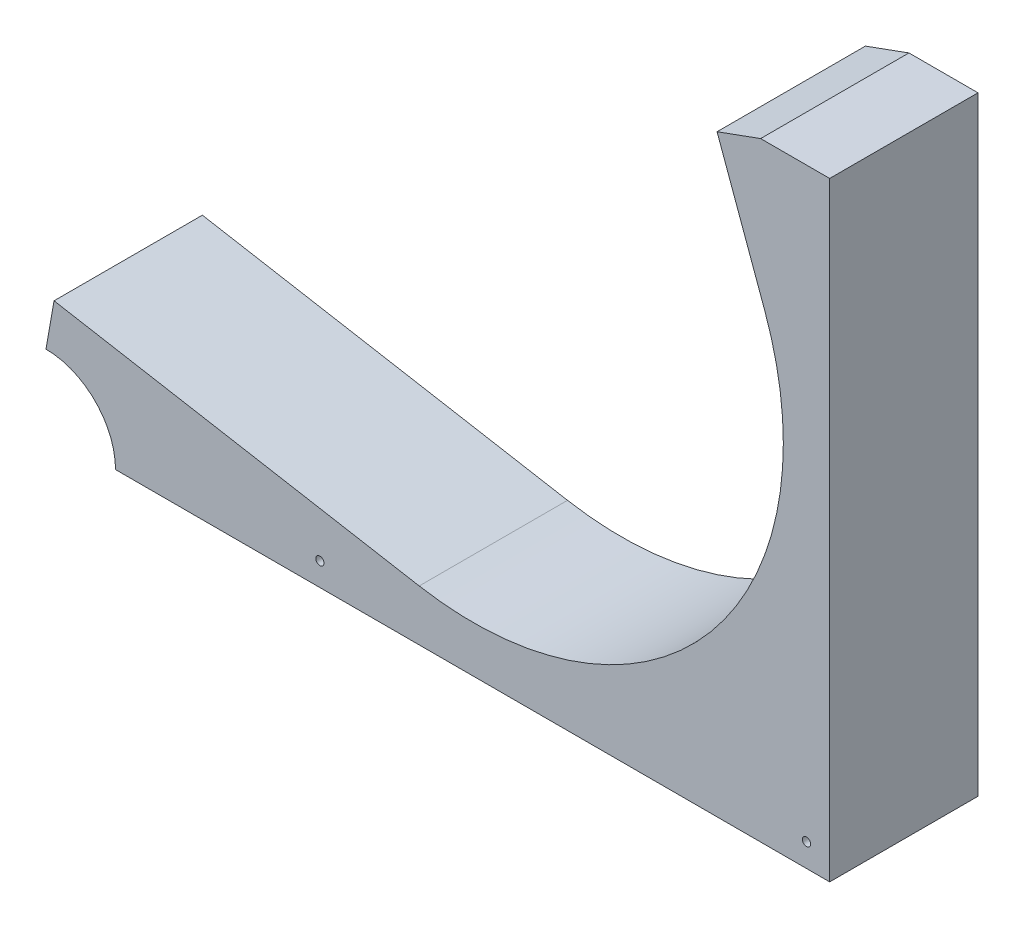
SolidWorks part; units mm, degrees
ref_plane "Front Plane" through (0, 0, 0) normal (0, 0, 1) x (1, 0, 0)
ref_plane "Top Plane" through (0, 0, 0) normal (0, 1, 0) x (1, 0, 0)
ref_plane "Right Plane" through (0, 0, 0) normal (1, 0, 0) x (0, 0, -1)
sketch "Sketch2" plane through (0, 0, 0) normal (0, 0, 1) x (1, 0, 0)
  line L0 (0, 0) -> (69.3863, 0)
  line L1 (69.3863, 0) -> (61.2697, 22.3003)
  line L2 (0, -65.2018) -> (-81.9123, -65.2018) construction
  line L3 (-11.3222, -64.2112) -> (-111.3786, -46.5686)
  line L4 (61.2697, 22.3003) -> (48.2387, 58.1026)
  arc A0 (61.2697, 22.3003) -> (-11.3222, -64.2112) centre (0, 0) cw
  circle A1 centre (0, 0) radius 45.212 construction
  point P11 (-11.3222, -64.2112)
  dimension "D3" = 90.424
  dimension "D1" = 65.2018
  dimension "D2" = 70
  dimension "D4" = 10
  dimension "D5" = 38.1
  dimension "D6" = 101.6
sketch3d "3DSketch1"
  line L0 (-114.819, -66.0796, 0) -> (-111.3786, -46.5686, 0) construction
  line L1 (-117.0243, -78.5867, -20.32) -> (-114.819, -66.0796, -20.32)
  line L2 (-117.0243, -78.5867, -20.32) -> (-117.0243, -78.5867, 20.32)
  line L3 (-117.0243, -78.5867, 20.32) -> (-114.819, -66.0796, 20.32)
  line L4 (-114.819, -66.0796, -20.32) -> (-114.819, -66.0796, 20.32)
  line L5 (-117.0243, -78.5867, -20.32) -> (-114.819, -66.0796, 20.32) construction
  line L6 (-117.0243, -78.5867, 20.32) -> (-114.819, -66.0796, -20.32) construction
  line L7 (-11.3222, -64.2112, 0) -> (-111.3786, -46.5686, 0) construction
  line L8 (0, -65.2018, 0) -> (-81.9123, -65.2018, 0) construction
  point P4 (-115.9216, -72.3331, 0)
  dimension "D1" = 12.7
  dimension "D2" = 40.64
  dimension "D3" = 19.812
sweep "Sweep3" add profiles "3DSketch1" path "Sketch2"
sketch "Sketch5" plane through (0, 0, 20.32) normal (0, 0, 1) x (1, 0, 0)
  line L0 (-117.0243, -78.5867) -> (-117.0243, -97.7138)
  line L1 (-117.0243, -97.7138) -> (97.7138, -97.7138)
  line L2 (97.7138, -97.7138) -> (97.7138, 69.2224)
  line L3 (97.7138, 69.2224) -> (78.79, 69.2224)
  line L4 (-117.0243, -78.5867) -> (-16.9678, -96.2293)
  line L5 (91.8209, 33.4201) -> (78.79, 69.2224)
  arc A0 (-16.9678, -96.2293) -> (91.8209, 33.4201) centre (0, 0) ccw construction
  arc A1 (-16.9678, -96.2293) -> (91.8209, 33.4201) centre (0, 0) ccw
  line M7 (-117.0243, -78.5867) -> (-16.9678, -96.2293)
extrude "Boss-Extrude1" add sketch "Sketch5" against normal up to surface (40.64 mm away) contours A1 L0 L1 M7 | A1 L1 L2 | A1 L2 L3 L5 up to face at (-65.8934, -81.1545, -20.32)
sketch "Sketch6" plane through (0, 0, 20.32) normal (0, 0, 1) x (1, 0, 0)
  circle A0 centre (91.3638, -91.3638) radius 1.1303 construction
  circle A1 centre (-41.9735, -91.3638) radius 1.1303 construction
  circle A2 centre (91.3638, -91.3638) radius 1.1303
  circle A3 centre (-41.9735, -91.3638) radius 1.1303
extrude "Cut-Extrude1" cut sketch "Sketch6" against normal through all
sketch "Sketch7" plane through (0, 0, 20.32) normal (0, 0, 1) x (1, 0, 0)
  circle A0 centre (-117.0243, -97.7138) radius 19.05
  dimension "D1" = 38.1
extrude "Cut-Extrude2" cut sketch "Sketch7" against normal through all
